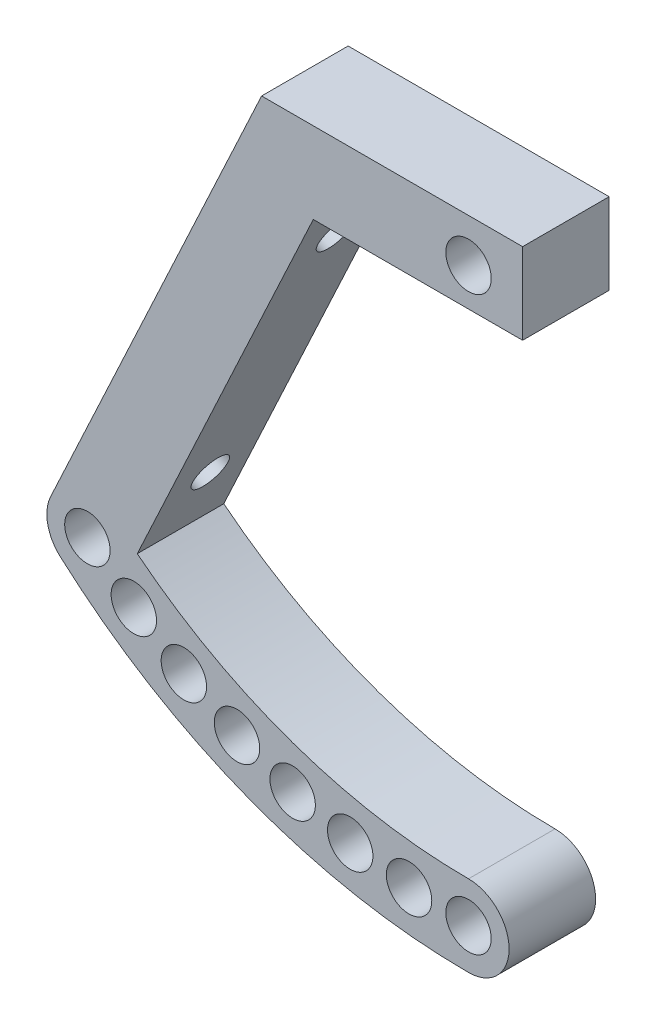
SolidWorks part; units mm, degrees
ref_plane "Front Plane" through (0, 0, 0) normal (0, 0, 1) x (1, 0, 0)
ref_plane "Top Plane" through (0, 0, 0) normal (0, 1, 0) x (1, 0, 0)
ref_plane "Right Plane" through (0, 0, 0) normal (1, 0, 0) x (0, 0, -1)
sketch "Sketch1" plane through (0, 0, 0) normal (0, 0, 1) x (1, 0, 0)
  line L0 (-26.3199, 30.1475) -> (-21.407, 27.6582) construction
  line L1 (-21.407, 27.6582) -> (-16.2619, 25.6935) construction
  line L2 (-16.2619, 25.6935) -> (-10.9403, 24.2748) construction
  line L3 (-10.9403, 24.2748) -> (-5.5, 23.4173) construction
  line L4 (-5.5, 23.4173) -> (0, 23.1304) construction
  line L5 (-35.2385, 36.5863) -> (-30.9471, 33.1343) construction
  line L6 (-30.9471, 33.1343) -> (-26.3199, 30.1475) construction
  line L7 (5, 72.5) -> (-19.132, 72.5)
  line L8 (5, 72.5) -> (5, 80)
  line L9 (-19.132, 72.5) -> (-19.132, 80)
  line L10 (5, 80) -> (-19.132, 80)
  line L12 (-19.132, 80) -> (-40.2876, 34.6316)
  line L13 (-19.132, 80) -> (-12.3347, 76.8304)
  line L14 (-40.2876, 34.6316) -> (-33.4903, 31.462)
  line L15 (-12.3347, 76.8304) -> (-33.4903, 31.462)
  line L16 (-15.7333, 78.4152) -> (-36.889, 33.0468) construction
  circle A0 centre (0, 76) radius 2.1
  circle A1 centre (0, 23.1304) radius 2.1
  arc A4 (0, 23.1304) -> (-35.2385, 36.5863) centre (0, 76) cw construction
  arc A5 (-37.7379, 33.7907) -> (0, 19.3804) centre (0, 76) ccw
  arc A6 (-32.739, 39.3819) -> (0, 26.8804) centre (0, 76) ccw
  arc A7 (-32.739, 39.3819) -> (-37.7379, 33.7907) centre (-35.2385, 36.5863) ccw
  arc A8 (0, 19.3804) -> (0, 26.8804) centre (0, 23.1304) ccw
  circle A9 centre (-5.5, 23.4173) radius 2.1
  circle A10 centre (-10.9403, 24.2748) radius 2.1
  circle A11 centre (-16.2619, 25.6935) radius 2.1
  circle A12 centre (-21.407, 27.6582) radius 2.1
  circle A13 centre (-26.3199, 30.1475) radius 2.1
  circle A14 centre (-30.9471, 33.1343) radius 2.1
  circle A15 centre (-35.2385, 36.5863) radius 2.1
  point P12 (-18.8601, 26.6088)
  point P40 (-15.138, 82.2601)
  point P41 (-16.2817, 80.4792)
  point P43 (-12.7199, 78.1918)
  point P46 (-7.066, 80)
  point P49 (-15.7828, 80)
  point P50 (-18.9497, 80)
  point P51 (-37.7379, 31.9757)
  dimension "D1" = 7.5
  dimension "D2" = 5.5
  dimension "D3" = 7.5
  dimension "D4" = 115
extrude "Boss-Extrude1" add sketch "Sketch1" along normal blind 8 contours L13 L15 L7 L8 L10 A0 | L15 L13 L9 L7 | A7 A6 L15 L7 L9 L12 | A14 L15 A6 A7 A5 L14 A15 | A14 L15 L14 A5 A8 A6 A13 A12 A11 A10 A9 A1
ref_plane "Plane2" through (-46.5966, -82.6195, -9.525) normal (0, 0, -1) x (-0.7889, 0.6145, 0)
sketch "Sketch2" plane through (-46.3567, 21.6165, 0) normal (-0.9063, 0.4226, 0) x (0, 0, 1)
  line L0 (4, 64.4191) -> (4, 18.266) construction
  line L1 (8, 64.4191) -> (0, 64.4191) construction
  line L2 (8, 18.266) -> (0, 18.266) construction
  line L3 (4, 55.0426) -> (0, 64.4191) construction
  line L4 (4, 27.6426) -> (0, 18.266) construction
  circle A0 centre (4, 55.0426) radius 1.65
  circle A1 centre (4, 27.6426) radius 1.65
  dimension "D1" = 3.3
  dimension "D2" = 27.4
extrude "Cut-Extrude1" cut sketch "Sketch2" against normal up to next
